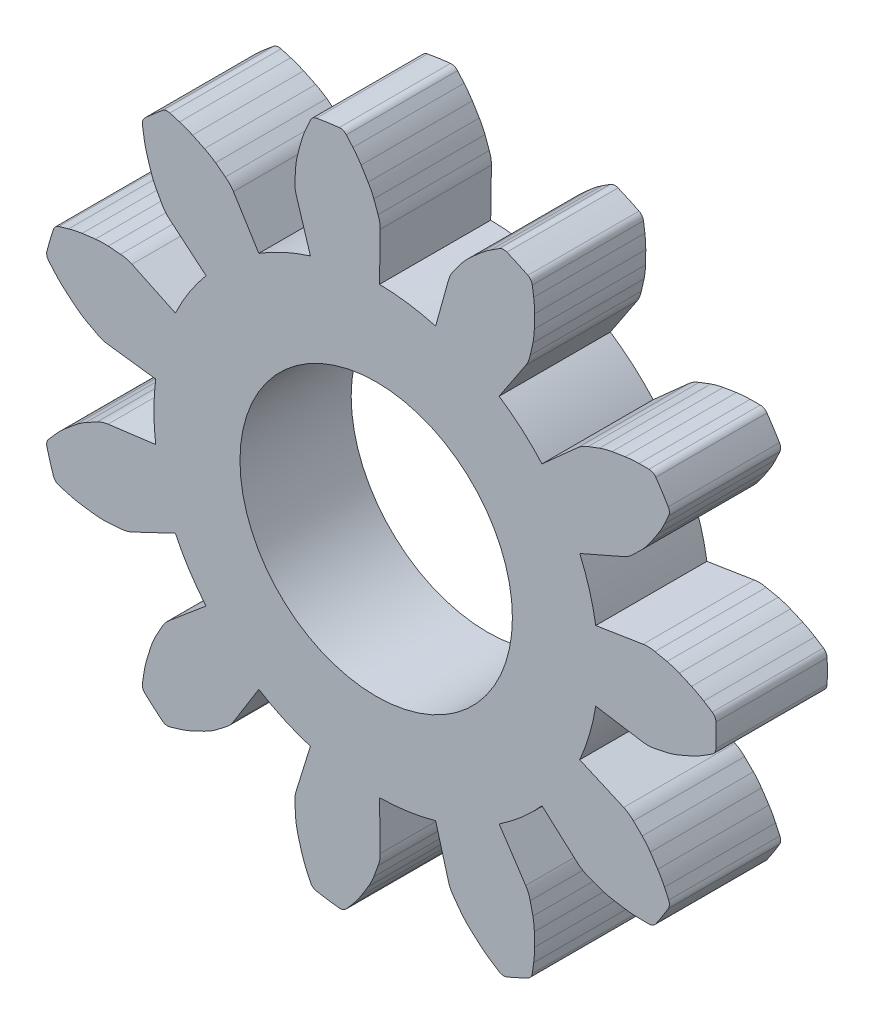
SolidWorks part; units mm, degrees
ref_plane "Front Plane" through (0, 0, 0) normal (0, 0, 1) x (1, 0, 0)
ref_plane "Top Plane" through (0, 0, 0) normal (0, 1, 0) x (1, 0, 0)
ref_plane "Right Plane" through (0, 0, 0) normal (1, 0, 0) x (0, 0, -1)
sketch "Model" plane through (0, 0, 0) normal (0, 0, 1) x (1, 0, 0)
  line L0 (12.7175, 8.3593) -> (13.5706, 8.495)
  line L1 (12.7175, 7.1035) -> (13.5706, 6.9678)
  line L2 (12.4301, 6.1249) -> (13.2212, 5.7778)
  line L3 (11.7512, 5.0684) -> (12.3956, 4.493)
  line L4 (10.9804, 4.4005) -> (11.4582, 3.6808)
  line L5 (9.8381, 3.8789) -> (10.0691, 3.0464)
  line L6 (8.8285, 3.7337) -> (8.8414, 2.8699)
  line L7 (7.5855, 3.9124) -> (7.3298, 3.0872)
  line L8 (6.6577, 4.3361) -> (6.2016, 3.6025)
  line L9 (5.7087, 5.1585) -> (5.0474, 4.6026)
  line L10 (5.1573, 6.0165) -> (4.3769, 5.646)
  line L11 (4.8034, 7.2215) -> (3.9466, 7.1113)
  line L12 (4.8034, 8.2414) -> (3.9466, 8.3515)
  line L13 (5.1573, 9.4463) -> (4.3769, 9.8169)
  line L14 (5.7087, 10.3043) -> (5.0474, 10.8602)
  line L15 (6.6577, 11.1267) -> (6.2016, 11.8603)
  line L16 (7.5855, 11.5504) -> (7.3298, 12.3756)
  line L17 (8.8285, 11.7291) -> (8.8414, 12.5929)
  line L18 (9.8381, 11.584) -> (10.0691, 12.4164)
  line L19 (10.9804, 11.0623) -> (11.4582, 11.782)
  line L20 (11.7512, 10.3944) -> (12.3956, 10.9698)
  line L21 (12.4301, 9.3379) -> (13.2212, 9.685)
  arc A0 (12.7175, 8.3593) -> (12.6051, 8.8578) centre (8.7689, 7.7314) ccw
  arc A1 (13.7832, 8.4865) -> (13.5706, 8.495) centre (13.6558, 7.9595) ccw
  arc A2 (14.0006, 8.4412) -> (13.7832, 8.4865) centre (-129.6875, -679.4336) ccw
  arc A3 (14.2202, 8.369) -> (14.0006, 8.4412) centre (13.66, 7.0347) ccw
  arc A4 (14.4404, 8.2731) -> (14.2202, 8.369) centre (10.8047, 0.2239) ccw
  arc A5 (14.6597, 8.1552) -> (14.4404, 8.2731) centre (13.6917, 6.6176) ccw
  arc A6 (14.8126, 8.0579) -> (14.6597, 8.1552) centre (5.9522, -5.6973) ccw
  arc A7 (14.8838, 7.7314) -> (14.8802, 7.9387) centre (8.7689, 7.7314) ccw
  arc A8 (14.8802, 7.9387) -> (14.8126, 8.0579) centre (14.7326, 7.9337) ccw
  arc A9 (12.6051, 6.605) -> (12.7175, 7.1035) centre (8.7689, 7.7314) ccw
  arc A10 (13.5706, 6.9678) -> (13.7832, 6.9763) centre (13.6558, 7.5033) ccw
  arc A11 (13.7832, 6.9763) -> (14.0006, 7.0217) centre (-129.6875, 694.8964) ccw
  arc A12 (14.0006, 7.0217) -> (14.2202, 7.0938) centre (13.66, 8.4282) ccw
  arc A13 (14.2202, 7.0938) -> (14.4404, 7.1897) centre (10.8047, 15.2389) ccw
  arc A14 (14.4404, 7.1897) -> (14.6597, 7.3076) centre (13.6917, 8.8452) ccw
  arc A15 (14.6597, 7.3076) -> (14.8126, 7.4049) centre (5.9522, 21.1601) ccw
  arc A16 (14.8802, 7.5241) -> (14.8838, 7.7314) centre (8.7689, 7.7314) ccw
  arc A17 (14.8126, 7.4049) -> (14.8802, 7.5241) centre (14.7326, 7.5291) ccw
  arc A18 (12.4301, 6.1249) -> (12.6051, 6.605) centre (8.7689, 7.7314) ccw
  arc A19 (13.3955, 5.6557) -> (13.2212, 5.7778) centre (13.0033, 5.2813) ccw
  arc A20 (13.5539, 5.5) -> (13.3955, 5.6557) centre (-479.2175, -495.4934) ccw
  arc A21 (13.6995, 5.3206) -> (13.5539, 5.5) centre (12.5069, 4.501) ccw
  arc A22 (13.8329, 5.1209) -> (13.6995, 5.3206) centre (6.4227, 0.3151) ccw
  arc A23 (13.9537, 4.9031) -> (13.8329, 5.1209) centre (12.3081, 4.133) ccw
  arc A24 (14.0297, 4.7387) -> (13.9537, 4.9031) centre (-0.8607, -2.0427) ccw
  arc A25 (13.9131, 4.4255) -> (14.0222, 4.6018) centre (8.7689, 7.7314) ccw
  arc A26 (14.0222, 4.6018) -> (14.0297, 4.7387) centre (13.8952, 4.6774) ccw
  arc A27 (11.3872, 4.7098) -> (11.7512, 5.0684) centre (8.7689, 7.7314) ccw
  arc A28 (12.3956, 4.493) -> (12.579, 4.3852) centre (12.7567, 4.8975) ccw
  arc A29 (12.579, 4.3852) -> (12.7864, 4.3059) centre (263.8014, 660.6666) ccw
  arc A30 (12.7864, 4.3059) -> (13.0101, 4.2479) centre (13.2603, 5.6732) ccw
  arc A31 (13.0101, 4.2479) -> (13.2472, 4.2095) centre (14.5404, 12.9465) ccw
  arc A32 (13.2472, 4.2095) -> (13.4955, 4.1901) centre (13.5124, 6.007) ccw
  arc A33 (13.4955, 4.1901) -> (13.6766, 4.1893) centre (13.6595, 20.5512) ccw
  arc A34 (13.798, 4.253) -> (13.9131, 4.4255) centre (8.7689, 7.7314) ccw
  arc A35 (13.6766, 4.1893) -> (13.798, 4.253) centre (13.6765, 4.3371) ccw
  arc A36 (10.9804, 4.4005) -> (11.3872, 4.7098) centre (8.7689, 7.7314) ccw
  arc A37 (11.5388, 3.4839) -> (11.4582, 3.6808) centre (11.0065, 3.3809) ccw
  arc A38 (11.5879, 3.2673) -> (11.5388, 3.4839) centre (-673.8153, -151.7828) ccw
  arc A39 (11.6134, 3.0376) -> (11.5879, 3.2673) centre (10.167, 2.9929) ccw
  arc A40 (11.6177, 2.7976) -> (11.6134, 3.0376) centre (2.7855, 2.7609) ccw
  arc A41 (11.6016, 2.549) -> (11.6177, 2.7976) centre (9.8008, 2.7908) ccw
  arc A42 (11.5766, 2.3696) -> (11.6016, 2.549) centre (-4.6163, 4.7151) ccw
  arc A43 (11.3091, 2.1692) -> (11.4962, 2.2585) centre (8.7689, 7.7314) ccw
  arc A44 (11.4962, 2.2585) -> (11.5766, 2.3696) centre (11.4303, 2.3908) ccw
  arc A45 (9.3379, 3.774) -> (9.8381, 3.8789) centre (8.7689, 7.7314) ccw
  arc A46 (10.0691, 3.0464) -> (10.1651, 2.8566) centre (10.5915, 3.1914) ccw
  arc A47 (10.1651, 2.8566) -> (10.2967, 2.6776) centre (576.3193, 419.1345) ccw
  arc A48 (10.2967, 2.6776) -> (10.4535, 2.5079) centre (11.4345, 3.5718) ccw
  arc A49 (10.4535, 2.5079) -> (10.6322, 2.3475) centre (16.4437, 8.9984) ccw
  arc A50 (10.6322, 2.3475) -> (10.8306, 2.1969) centre (11.8271, 3.7162) ccw
  arc A51 (10.8306, 2.1969) -> (10.9825, 2.0983) centre (19.814, 15.8721) ccw
  arc A52 (11.1191, 2.0863) -> (11.3091, 2.1692) centre (8.7689, 7.7314) ccw
  arc A53 (10.9825, 2.0983) -> (11.1191, 2.0863) centre (11.0623, 2.2227) ccw
  arc A54 (8.8285, 3.7337) -> (9.3379, 3.774) centre (8.7689, 7.7314) ccw
  arc A55 (8.8028, 2.6607) -> (8.8414, 2.8699) centre (8.2992, 2.8618) ccw
  arc A56 (8.7269, 2.4519) -> (8.8028, 2.6607) centre (-651.6973, 242.5724) ccw
  arc A57 (8.6242, 2.2449) -> (8.7269, 2.4519) centre (7.3832, 2.9893) ccw
  arc A58 (8.498, 2.0406) -> (8.6242, 2.2449) centre (1.0481, 6.7848) ccw
  arc A59 (8.3501, 1.8403) -> (8.498, 2.0406) centre (6.9659, 3.0173) ccw
  arc A60 (8.232, 1.7028) -> (8.3501, 1.8403) centre (-4.1222, 12.4306) ccw
  arc A61 (7.8987, 1.6788) -> (8.1044, 1.6528) centre (8.7689, 7.7314) ccw
  arc A62 (8.1044, 1.6528) -> (8.232, 1.7028) centre (8.1205, 1.7997) ccw
  arc A63 (7.1081, 4.0946) -> (7.5855, 3.9124) centre (8.7689, 7.7314) ccw
  arc A64 (7.3298, 3.0872) -> (7.3079, 2.8756) centre (7.8477, 2.9268) ccw
  arc A65 (7.3079, 2.8756) -> (7.3219, 2.654) centre (708.644, 46.9848) ccw
  arc A66 (7.3219, 2.654) -> (7.3621, 2.4264) centre (8.7625, 2.791) ccw
  arc A67 (7.3621, 2.4264) -> (7.4256, 2.1948) centre (15.9103, 4.6479) ccw
  arc A68 (7.4256, 2.1948) -> (7.5111, 1.9609) centre (9.1708, 2.7002) ccw
  arc A69 (7.5111, 1.9609) -> (7.5856, 1.7958) centre (22.4618, 8.6084) ccw
  arc A70 (7.694, 1.7118) -> (7.8987, 1.6788) centre (8.7689, 7.7314) ccw
  arc A71 (7.5856, 1.7958) -> (7.694, 1.7118) centre (7.72, 1.8573) ccw
  arc A72 (6.6577, 4.3361) -> (7.1081, 4.0946) centre (8.7689, 7.7314) ccw
  arc A73 (6.056, 3.4474) -> (6.2016, 3.6025) centre (5.7411, 3.8888) ccw
  arc A74 (5.8793, 3.3128) -> (6.056, 3.4474) centre (-419.886, 562.3672) ccw
  arc A75 (5.681, 3.1941) -> (5.8793, 3.3128) centre (5.0394, 4.4913) ccw
  arc A76 (5.4644, 3.0905) -> (5.681, 3.1941) centre (1.762, 11.1093) ccw
  arc A77 (5.2316, 3.0019) -> (5.4644, 3.0905) centre (4.7035, 4.7404) ccw
  arc A78 (5.058, 2.9501) -> (5.2316, 3.0019) centre (0.4648, 18.6541) ccw
  arc A79 (4.7646, 3.1101) -> (4.9236, 2.977) centre (8.7689, 7.7314) ccw
  arc A80 (4.9236, 2.977) -> (5.058, 2.9501) centre (5.0165, 3.0919) ccw
  arc A81 (5.4055, 5.5698) -> (5.7087, 5.1585) centre (8.7689, 7.7314) ccw
  arc A82 (5.0474, 4.6026) -> (4.9146, 4.4364) centre (5.3964, 4.1875) ccw
  arc A83 (4.9146, 4.4364) -> (4.8065, 4.2423) centre (618.7633, -337.6276) ccw
  arc A84 (4.8065, 4.2423) -> (4.7173, 4.0291) centre (6.0925, 3.5787) ccw
  arc A85 (4.7173, 4.0291) -> (4.6455, 3.8) centre (13.1096, 1.2765) ccw
  arc A86 (4.6455, 3.8) -> (4.591, 3.557) centre (6.387, 3.2816) ccw
  arc A87 (4.591, 3.557) -> (4.5644, 3.3778) centre (20.7622, 1.0662) ccw
  arc A88 (4.6102, 3.2486) -> (4.7646, 3.1101) centre (8.7689, 7.7314) ccw
  arc A89 (4.5644, 3.3778) -> (4.6102, 3.2486) centre (4.7107, 3.3569) ccw
  arc A90 (5.1573, 6.0165) -> (5.4055, 5.5698) centre (8.7689, 7.7314) ccw
  arc A91 (4.1705, 5.5942) -> (4.3769, 5.646) centre (4.1443, 6.1358) ccw
  arc A92 (3.9491, 5.5765) -> (4.1705, 5.5942) centre (-51.9798, 706.0691) ccw
  arc A93 (3.7181, 5.5839) -> (3.9491, 5.5765) centre (3.8797, 7.022) ccw
  arc A94 (3.4799, 5.6138) -> (3.7181, 5.5839) centre (4.7005, 14.3613) ccw
  arc A95 (3.2362, 5.6652) -> (3.4799, 5.6138) centre (3.7318, 7.4132) ccw
  arc A96 (3.0621, 5.7154) -> (3.2362, 5.6652) centre (7.6883, 21.4097) ccw
  arc A97 (2.9018, 6.0087) -> (2.9636, 5.8107) centre (8.7689, 7.7314) ccw
  arc A98 (2.9636, 5.8107) -> (3.0621, 5.7154) centre (3.1039, 5.8572) ccw
  arc A99 (4.7708, 7.7314) -> (4.8034, 7.2215) centre (8.7689, 7.7314) ccw
  arc A100 (3.9466, 7.1113) -> (3.745, 7.0433) centre (4.0158, 6.5735) ccw
  arc A101 (3.745, 7.0433) -> (3.5492, 6.9385) centre (335.2137, -612.5909) ccw
  arc A102 (3.5492, 6.9385) -> (3.3589, 6.8074) centre (4.2723, 5.6849) ccw
  arc A103 (3.3589, 6.8074) -> (3.1746, 6.6534) centre (8.9308, -0.0455) ccw
  arc A104 (3.1746, 6.6534) -> (2.9974, 6.4784) centre (4.3594, 5.2758) ccw
  arc A105 (2.9974, 6.4784) -> (2.8781, 6.342) centre (15.2549, -4.3598) ccw
  arc A106 (2.8468, 6.2086) -> (2.9018, 6.0087) centre (8.7689, 7.7314) ccw
  arc A107 (2.8781, 6.342) -> (2.8468, 6.2086) centre (2.9899, 6.2454) ccw
  arc A108 (4.8034, 8.2414) -> (4.7708, 7.7314) centre (8.7689, 7.7314) ccw
  arc A109 (3.745, 8.4196) -> (3.9466, 8.3515) centre (4.0158, 8.8893) ccw
  arc A110 (3.5492, 8.5244) -> (3.745, 8.4196) centre (335.2137, 628.0537) ccw
  arc A111 (3.3589, 8.6555) -> (3.5492, 8.5244) centre (4.2723, 9.7779) ccw
  arc A112 (3.1746, 8.8094) -> (3.3589, 8.6555) centre (8.9308, 15.5084) ccw
  arc A113 (2.9974, 8.9844) -> (3.1746, 8.8094) centre (4.3594, 10.187) ccw
  arc A114 (2.8781, 9.1208) -> (2.9974, 8.9844) centre (15.2549, 19.8226) ccw
  arc A115 (2.9018, 9.4542) -> (2.8468, 9.2542) centre (8.7689, 7.7314) ccw
  arc A116 (2.8468, 9.2542) -> (2.8781, 9.1208) centre (2.9899, 9.2174) ccw
  arc A117 (5.4055, 9.893) -> (5.1573, 9.4463) centre (8.7689, 7.7314) ccw
  arc A118 (4.3769, 9.8169) -> (4.1705, 9.8686) centre (4.1443, 9.327) ccw
  arc A119 (4.1705, 9.8686) -> (3.9491, 9.8863) centre (-51.9798, -690.6063) ccw
  arc A120 (3.9491, 9.8863) -> (3.7181, 9.879) centre (3.8797, 8.4409) ccw
  arc A121 (3.7181, 9.879) -> (3.4799, 9.849) centre (4.7005, 1.1015) ccw
  arc A122 (3.4799, 9.849) -> (3.2362, 9.7977) centre (3.7318, 8.0496) ccw
  arc A123 (3.2362, 9.7977) -> (3.0621, 9.7474) centre (7.6883, -5.9469) ccw
  arc A124 (2.9636, 9.6521) -> (2.9018, 9.4542) centre (8.7689, 7.7314) ccw
  arc A125 (3.0621, 9.7474) -> (2.9636, 9.6521) centre (3.1039, 9.6057) ccw
  arc A126 (5.7087, 10.3043) -> (5.4055, 9.893) centre (8.7689, 7.7314) ccw
  arc A127 (4.9146, 11.0265) -> (5.0474, 10.8602) centre (5.3964, 11.2753) ccw
  arc A128 (4.8065, 11.2205) -> (4.9146, 11.0265) centre (618.7633, 353.0904) ccw
  arc A129 (4.7173, 11.4337) -> (4.8065, 11.2205) centre (6.0925, 11.8841) ccw
  arc A130 (4.6455, 11.6628) -> (4.7173, 11.4337) centre (13.1096, 14.1863) ccw
  arc A131 (4.591, 11.9059) -> (4.6455, 11.6628) centre (6.387, 12.1812) ccw
  arc A132 (4.5644, 12.0851) -> (4.591, 11.9059) centre (20.7622, 14.3966) ccw
  arc A133 (4.7646, 12.3527) -> (4.6102, 12.2143) centre (8.7689, 7.7314) ccw
  arc A134 (4.6102, 12.2143) -> (4.5644, 12.0851) centre (4.7107, 12.1059) ccw
  arc A135 (7.1081, 11.3683) -> (6.6577, 11.1267) centre (8.7689, 7.7314) ccw
  arc A136 (6.2016, 11.8603) -> (6.056, 12.0155) centre (5.7411, 11.574) ccw
  arc A137 (6.056, 12.0155) -> (5.8793, 12.1501) centre (-419.886, -546.9044) ccw
  arc A138 (5.8793, 12.1501) -> (5.681, 12.2687) centre (5.0394, 10.9716) ccw
  arc A139 (5.681, 12.2687) -> (5.4644, 12.3723) centre (1.762, 4.3536) ccw
  arc A140 (5.4644, 12.3723) -> (5.2316, 12.4609) centre (4.7035, 10.7224) ccw
  arc A141 (5.2316, 12.4609) -> (5.058, 12.5127) centre (0.4648, -3.1913) ccw
  arc A142 (4.9236, 12.4858) -> (4.7646, 12.3527) centre (8.7689, 7.7314) ccw
  arc A143 (5.058, 12.5127) -> (4.9236, 12.4858) centre (5.0165, 12.3709) ccw
  arc A144 (7.5855, 11.5504) -> (7.1081, 11.3683) centre (8.7689, 7.7314) ccw
  arc A145 (7.3079, 12.5872) -> (7.3298, 12.3756) centre (7.8477, 12.5361) ccw
  arc A146 (7.3219, 12.8089) -> (7.3079, 12.5872) centre (708.644, -31.522) ccw
  arc A147 (7.3621, 13.0365) -> (7.3219, 12.8089) centre (8.7625, 12.6718) ccw
  arc A148 (7.4256, 13.268) -> (7.3621, 13.0365) centre (15.9103, 10.8149) ccw
  arc A149 (7.5111, 13.5019) -> (7.4256, 13.268) centre (9.1708, 12.7626) ccw
  arc A150 (7.5856, 13.6671) -> (7.5111, 13.5019) centre (22.4618, 6.8545) ccw
  arc A151 (7.8987, 13.784) -> (7.694, 13.751) centre (8.7689, 7.7314) ccw
  arc A152 (7.694, 13.751) -> (7.5856, 13.6671) centre (7.72, 13.6055) ccw
  arc A153 (9.3379, 11.6889) -> (8.8285, 11.7291) centre (8.7689, 7.7314) ccw
  arc A154 (8.8414, 12.5929) -> (8.8028, 12.8021) centre (8.2992, 12.601) ccw
  arc A155 (8.8028, 12.8021) -> (8.7269, 13.0109) centre (-651.6973, -227.1096) ccw
  arc A156 (8.7269, 13.0109) -> (8.6242, 13.2179) centre (7.3832, 12.4735) ccw
  arc A157 (8.6242, 13.2179) -> (8.498, 13.4222) centre (1.0481, 8.678) ccw
  arc A158 (8.498, 13.4222) -> (8.3501, 13.6226) centre (6.9659, 12.4456) ccw
  arc A159 (8.3501, 13.6226) -> (8.232, 13.76) centre (-4.1222, 3.0323) ccw
  arc A160 (8.1044, 13.81) -> (7.8987, 13.784) centre (8.7689, 7.7314) ccw
  arc A161 (8.232, 13.76) -> (8.1044, 13.81) centre (8.1205, 13.6631) ccw
  arc A162 (9.8381, 11.584) -> (9.3379, 11.6889) centre (8.7689, 7.7314) ccw
  arc A163 (10.1651, 12.6063) -> (10.0691, 12.4164) centre (10.5915, 12.2714) ccw
  arc A164 (10.2967, 12.7852) -> (10.1651, 12.6063) centre (576.3193, -403.6717) ccw
  arc A165 (10.4535, 12.9549) -> (10.2967, 12.7852) centre (11.4345, 11.891) ccw
  arc A166 (10.6322, 13.1153) -> (10.4535, 12.9549) centre (16.4437, 6.4645) ccw
  arc A167 (10.8306, 13.2659) -> (10.6322, 13.1153) centre (11.8271, 11.7466) ccw
  arc A168 (10.9825, 13.3645) -> (10.8306, 13.2659) centre (19.814, -0.4093) ccw
  arc A169 (11.3091, 13.2936) -> (11.1191, 13.3766) centre (8.7689, 7.7314) ccw
  arc A170 (11.1191, 13.3766) -> (10.9825, 13.3645) centre (11.0623, 13.2401) ccw
  arc A171 (11.3872, 10.753) -> (10.9804, 11.0623) centre (8.7689, 7.7314) ccw
  arc A172 (11.4582, 11.782) -> (11.5388, 11.9789) centre (11.0065, 12.0819) ccw
  arc A173 (11.5388, 11.9789) -> (11.5879, 12.1955) centre (-673.8153, 167.2456) ccw
  arc A174 (11.5879, 12.1955) -> (11.6134, 12.4252) centre (10.167, 12.4699) ccw
  arc A175 (11.6134, 12.4252) -> (11.6177, 12.6653) centre (2.7855, 12.7019) ccw
  arc A176 (11.6177, 12.6653) -> (11.6016, 12.9138) centre (9.8008, 12.672) ccw
  arc A177 (11.6016, 12.9138) -> (11.5766, 13.0932) centre (-4.6163, 10.7477) ccw
  arc A178 (11.4962, 13.2043) -> (11.3091, 13.2936) centre (8.7689, 7.7314) ccw
  arc A179 (11.5766, 13.0932) -> (11.4962, 13.2043) centre (11.4303, 13.0721) ccw
  arc A180 (11.7512, 10.3944) -> (11.3872, 10.753) centre (8.7689, 7.7314) ccw
  arc A181 (12.579, 11.0776) -> (12.3956, 10.9698) centre (12.7567, 10.5653) ccw
  arc A182 (12.7864, 11.157) -> (12.579, 11.0776) centre (263.8014, -645.2038) ccw
  arc A183 (13.0101, 11.215) -> (12.7864, 11.157) centre (13.2603, 9.7896) ccw
  arc A184 (13.2472, 11.2533) -> (13.0101, 11.215) centre (14.5404, 2.5163) ccw
  arc A185 (13.4955, 11.2727) -> (13.2472, 11.2533) centre (13.5124, 9.4559) ccw
  arc A186 (13.6766, 11.2735) -> (13.4955, 11.2727) centre (13.6595, -5.0884) ccw
  arc A187 (13.9131, 11.0373) -> (13.798, 11.2098) centre (8.7689, 7.7314) ccw
  arc A188 (13.798, 11.2098) -> (13.6766, 11.2735) centre (13.6765, 11.1258) ccw
  arc A189 (12.6051, 8.8578) -> (12.4301, 9.3379) centre (8.7689, 7.7314) ccw
  arc A190 (13.2212, 9.685) -> (13.3955, 9.8071) centre (13.0033, 10.1816) ccw
  arc A191 (13.3955, 9.8071) -> (13.5539, 9.9628) centre (-479.2175, 510.9562) ccw
  arc A192 (13.5539, 9.9628) -> (13.6995, 10.1422) centre (12.5069, 10.9619) ccw
  arc A193 (13.6995, 10.1422) -> (13.8329, 10.3419) centre (6.4227, 15.1477) ccw
  arc A194 (13.8329, 10.3419) -> (13.9537, 10.5597) centre (12.3081, 11.3299) ccw
  arc A195 (13.9537, 10.5597) -> (14.0297, 10.7242) centre (-0.8607, 17.5055) ccw
  arc A196 (14.0222, 10.861) -> (13.9131, 11.0373) centre (8.7689, 7.7314) ccw
  arc A197 (14.0297, 10.7242) -> (14.0222, 10.861) centre (13.8952, 10.7854) ccw
extrude "Boss-Extrude1" add sketch "Model" along normal blind 2
sketch "Sketch2" plane through (0, 0, 2) normal (0, 0, 1) x (1, 0, 0)
  circle A0 centre (8.7689, 7.7314) radius 3.9981 construction
  circle A1 centre (8.7689, 7.7314) radius 2.45
  dimension "D1" = 4.9
extrude "Cut-Extrude1" cut sketch "Sketch2" against normal blind 2
